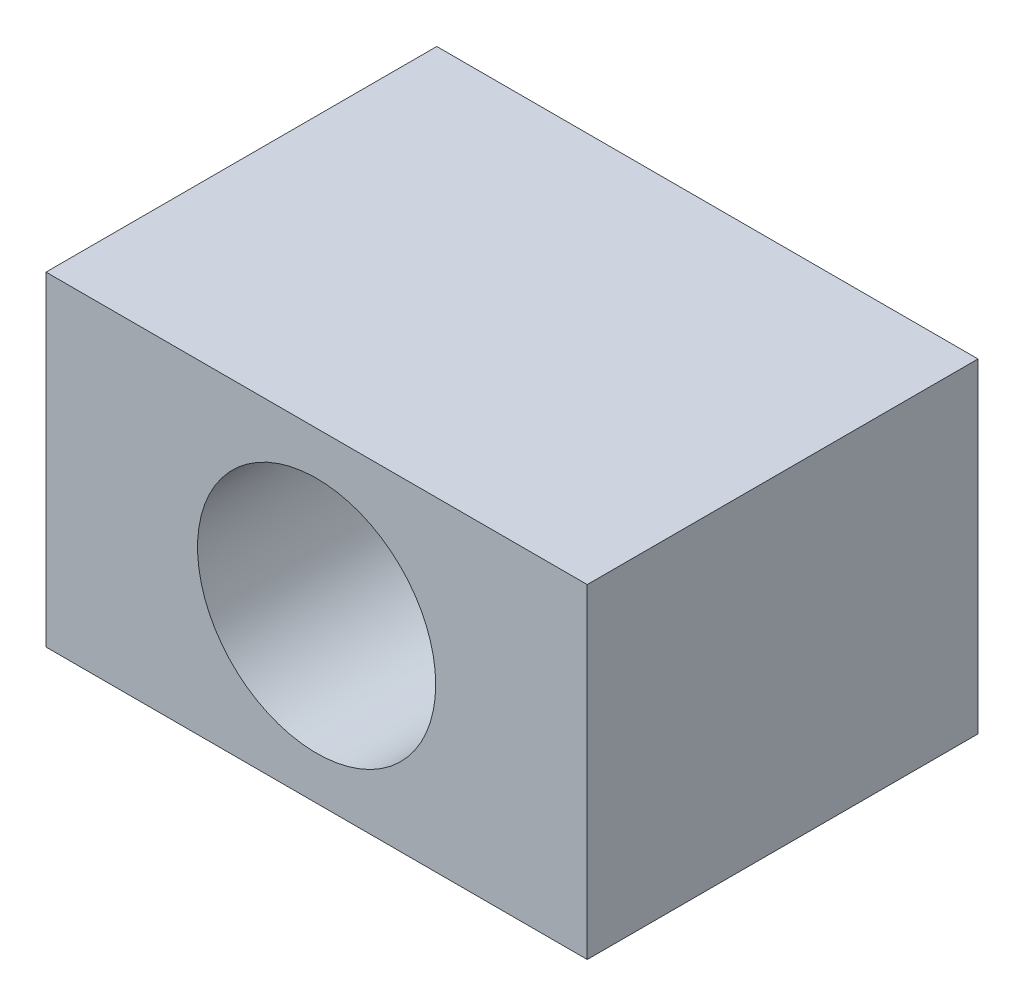
SolidWorks part; units mm, degrees
ref_plane "Front Plane" through (0, 0, 0) normal (0, 0, 1) x (1, 0, 0)
ref_plane "Top Plane" through (0, 0, 0) normal (0, 1, 0) x (1, 0, 0)
ref_plane "Right Plane" through (0, 0, 0) normal (1, 0, 0) x (0, 0, -1)
sketch "Sketch1" plane through (0, 0, 0) normal (0, 0, 1) x (1, 0, 0)
  line L0 (-15, 15) -> (15, 15)
  line L1 (-25, -15) -> (-25, 5)
  line L2 (-25, 5) -> (-15, 15) construction
  line L3 (-25, -15) -> (25, -15)
  line L4 (0, 15) -> (0, -17.0576) construction
  line L5 (25, -15) -> (25, 5)
  line L6 (25, 5) -> (15, 15) construction
  line L7 (15, 15) -> (25, 15)
  line L8 (25, 15) -> (25, 5)
  line L9 (-15, 15) -> (-25, 15)
  line L10 (-25, 15) -> (-25, 5)
  circle A0 centre (0, 0) radius 11
  dimension "D1" = 22
  dimension "D2" = 50
  dimension "D3" = 15
  dimension "D4" = 30
  dimension "D5" = 45
  dimension "D6" = 10
extrude "Boss-Extrude1" add sketch "Sketch1" along normal blind 36.1
sketch "Sketch3" plane through (0, -15, 0) normal (0, -1, 0) x (1, 0, 0)
  line L0 (-25, 36.1) -> (25, 0) construction
  line L2 (17.5, 6.05) -> (-17.5, 6.05) construction
  line L3 (17.5, 6.05) -> (17.5, 30.05) construction
  line L4 (17.5, 30.05) -> (-17.5, 30.05) construction
  line L5 (-17.5, 6.05) -> (-17.5, 30.05) construction
  line L6 (17.5, 6.05) -> (-17.5, 30.05) construction
  line L7 (17.5, 30.05) -> (-17.5, 6.05) construction
  circle A0 centre (-17.5, 30.05) radius 2.15
  circle A1 centre (17.5, 30.05) radius 2.15
  circle A2 centre (17.5, 6.05) radius 2.15
  circle A3 centre (-17.5, 6.05) radius 2.15
  point P4 (0, 18.05)
  dimension "D1" = 4.3
  dimension "D2" = 24
  dimension "D3" = 35
extrude "Cut-Extrude1" cut sketch "Sketch3" against normal blind 17
